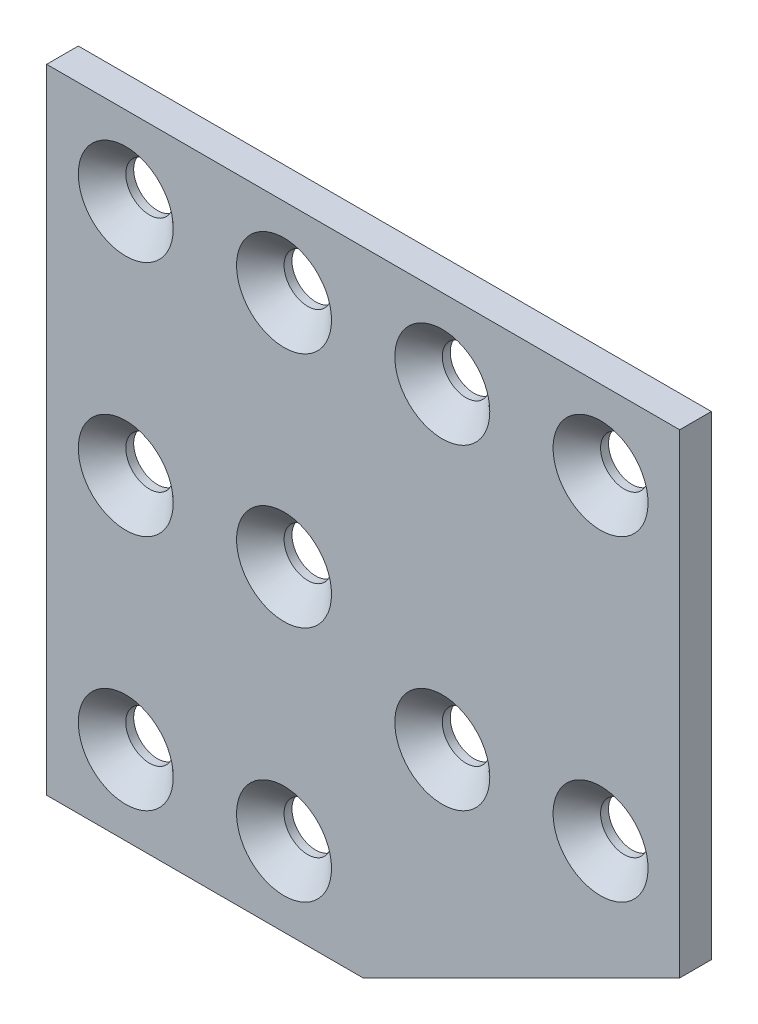
SolidWorks part; units mm, degrees
ref_plane "Front Plane" through (0, 0, 0) normal (0, 0, 1) x (1, 0, 0)
ref_plane "Top Plane" through (0, 0, 0) normal (0, 1, 0) x (1, 0, 0)
ref_plane "Right Plane" through (0, 0, 0) normal (1, 0, 0) x (0, 0, -1)
sketch "Sketch1" plane through (0, 0, 0) normal (0, 0, 1) x (1, 0, 0)
  line L0 (20, -40) -> (60, -20)
  line L1 (-20, -40) -> (20, -40)
  line L2 (-20, -40) -> (-20, 40)
  line L3 (-20, 40) -> (20, 40)
  line L4 (20, -40) -> (20, 40)
  line L5 (-20, -40) -> (20, 40) construction
  line L6 (-20, 40) -> (20, -40) construction
  line L7 (20, 40) -> (60, 40)
  line L8 (20, 40) -> (20, -20)
  line L9 (20, -20) -> (60, -20)
  line L10 (60, 40) -> (60, -20)
  point P0 (0, 0)
  point P9 (20, -1.5012)
  point P10 (20, 0)
  point P11 (20, -12.7646)
  dimension "D1" = 60
  dimension "D2" = 40
  dimension "D3" = 40
  dimension "D4" = 80
extrude "Boss-Extrude1" add sketch "Sketch1" along normal mid plane 4 contours L1 L4 L3 L2 | L9 L4 L0 | L10 L7 L4 L9
sketch "Sketch2" plane through (0, 0, 2) normal (0, 0, 1) x (1, 0, 0)
  line L0 (50, -10) -> (50, 30) construction
  line L1 (50, 30) -> (30, 30) construction
  line L2 (30, 30) -> (10, 30) construction
  line L3 (10, 30) -> (-10, 30) construction
  line L4 (-10, 30) -> (-10, 0) construction
  line L5 (-10, 0) -> (-10, -30) construction
  line L6 (-10, -30) -> (10, -30) construction
  line L7 (10, -30) -> (10, 0) construction
  line L8 (10, 0) -> (10, 30) construction
  line L9 (-10, 0) -> (0, 0) construction
  line L10 (0, 0) -> (10, 0) construction
  line L11 (30, 30) -> (30, -10) construction
  line L12 (30, -10) -> (50, -10) construction
  line L13 (-20, 40) -> (60, 40) construction
  line L14 (60, 40) -> (60, -20) construction
  circle A0 centre (50, 30) radius 3
  circle A1 centre (30, 30) radius 3
  circle A2 centre (50, -10) radius 3
  circle A3 centre (30, -10) radius 3
  circle A4 centre (-10, 30) radius 3
  circle A5 centre (10, 30) radius 3
  circle A6 centre (-10, 0) radius 3
  circle A7 centre (10, 0) radius 3
  circle A8 centre (-10, -30) radius 3
  circle A9 centre (10, -30) radius 3
  point P27 (-10, 0)
  point P28 (10, 0)
  point P29 (30, -10)
  point P30 (50, -10)
  point P31 (10, -30)
  point P32 (-10, -30)
  dimension "D1" = 6
  dimension "D2" = 10
  dimension "D3" = 10
  dimension "D4" = 10
  dimension "D5" = 20
extrude "Cut-Extrude1" cut sketch "Sketch2" against normal through all
chamfer "Chamfer1" distance 3 angle 45 10 edges at (13, -30, 2) (-7, -30, 2) (53, -10, 2) (33, -10, 2) (13, 0, 2) (-7, 0, 2) (53, 30, 2) (33, 30, 2) (13, 30, 2) (-7, 30, 2)
fillet "Fillet1" [suppressed] radius 1
